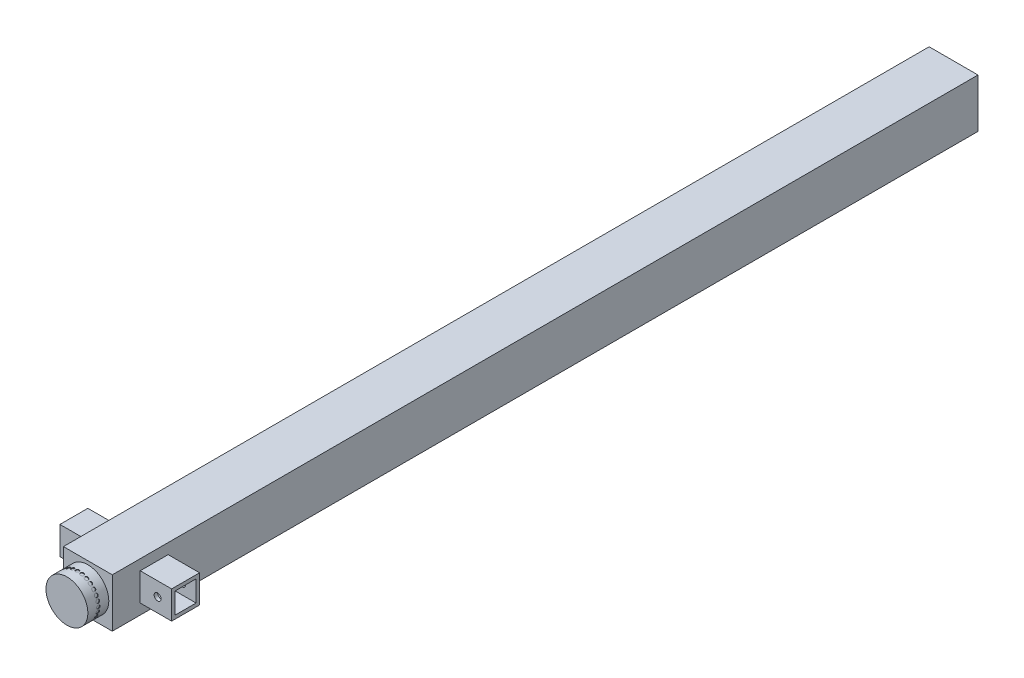
SolidWorks part; units mm, degrees
material "6061-T6 (SS)"
ref_plane "Front Plane" through (0, 0, 0) normal (0, 0, 1) x (1, 0, 0)
ref_plane "Top Plane" through (0, 0, 0) normal (0, 1, 0) x (1, 0, 0)
ref_plane "Right Plane" through (0, 0, 0) normal (1, 0, 0) x (0, 0, -1)
sketch "Sketch1" plane through (0, 0, 0) normal (0, 0, 1) x (1, 0, 0)
  line L0 (-38.1, 38.1) -> (-38.1, -38.1)
  line L1 (-44.45, 44.45) -> (44.45, 44.45)
  line L2 (-44.45, 44.45) -> (-44.45, -44.45)
  line L3 (-44.45, -44.45) -> (44.45, -44.45)
  line L4 (44.45, 44.45) -> (44.45, -44.45)
  line L5 (-44.45, 44.45) -> (44.45, -44.45) construction
  line L6 (-44.45, -44.45) -> (44.45, 44.45) construction
  line L7 (-38.1, -38.1) -> (38.1, -38.1)
  line L8 (38.1, 38.1) -> (38.1, -38.1)
  line L9 (-38.1, 38.1) -> (38.1, 38.1)
  point P0 (0, 0)
  dimension "D1" = 88.9
  dimension "D2" = 88.9
  dimension "D3" = 6.35
extrude "Boss-Extrude1" add sketch "Sketch1" against normal blind 1574.8
sketch "Sketch2" plane through (0, 44.45, 0) normal (0, 1, 0) x (1, 0, 0)
  line L0 (44.45, 1574.8) -> (44.45, 0) construction
  line L1 (-44.45, 6.35) -> (44.45, 6.35)
  line L2 (-44.45, 6.35) -> (-44.45, 0)
  line L3 (-44.45, 0) -> (44.45, 0)
  line L4 (44.45, 6.35) -> (44.45, 0)
  line L5 (-44.45, 6.35) -> (44.45, 0) construction
  line L6 (-44.45, 0) -> (44.45, 6.35) construction
  line L7 (44.45, 0) -> (-44.45, 0) construction
  line L8 (-44.45, 1574.8) -> (-44.45, 0) construction
  point P0 (0, 3.175)
  dimension "D1" = 6.35
extrude "Boss-Extrude2" add sketch "Sketch2" against normal up to surface (88.9 mm away) up to face at (0, -44.45, -787.4)
sketch "Sketch3" plane through (0, 0, 0) normal (0, 0, 1) x (1, 0, 0)
  circle A0 centre (0, 0) radius 38.1
  dimension "D1" = 76.2
extrude "Boss-Extrude3" add sketch "Sketch3" along normal blind 38.1
sketch "Sketch4" plane through (44.45, 0, 0) normal (1, 0, 0) x (0, 0, -1)
  line L0 (57.15, 19.05) -> (57.15, -19.05)
  line L1 (50.8, 25.4) -> (101.6, 25.4)
  line L2 (50.8, 25.4) -> (50.8, -25.4)
  line L3 (50.8, -25.4) -> (101.6, -25.4)
  line L4 (101.6, 25.4) -> (101.6, -25.4)
  line L5 (50.8, 25.4) -> (101.6, -25.4) construction
  line L6 (50.8, -25.4) -> (101.6, 25.4) construction
  line L7 (57.15, -19.05) -> (95.25, -19.05)
  line L8 (95.25, 19.05) -> (95.25, -19.05)
  line L9 (57.15, 19.05) -> (95.25, 19.05)
  point P0 (76.2, 0)
  point P5 (50.8, 0)
  dimension "D1" = 50.8
  dimension "D2" = 50.8
  dimension "D3" = 50.8
  dimension "D4" = 6.35
extrude "Boss-Extrude4" add sketch "Sketch4" along normal blind 57.15
sketch "Sketch5" plane through (-44.45, 0, 0) normal (-1, 0, 0) x (0, 0, 1)
  line L0 (0, 44.45) -> (0, -44.45) construction
  line L1 (-101.6, 25.4) -> (-50.8, 25.4)
  line L2 (-101.6, 25.4) -> (-101.6, -25.4)
  line L3 (-101.6, -25.4) -> (-50.8, -25.4)
  line L4 (-50.8, 25.4) -> (-50.8, -25.4)
  line L5 (-101.6, 25.4) -> (-50.8, -25.4) construction
  line L6 (-101.6, -25.4) -> (-50.8, 25.4) construction
  line L7 (-95.25, 19.05) -> (-95.25, -19.05)
  line L8 (-95.25, -19.05) -> (-57.15, -19.05)
  line L9 (-57.15, 19.05) -> (-57.15, -19.05)
  line L10 (-95.25, 19.05) -> (-57.15, 19.05)
  point P0 (-76.2, 0)
  dimension "D1" = 50.8
  dimension "D2" = 50.8
  dimension "D3" = 50.8
  dimension "D4" = 6.35
extrude "Boss-Extrude5" add sketch "Sketch5" along normal blind 57.15
sketch "Sketch7" plane through (-44.45, 0, 0) normal (-1, 0, 0) x (0, 0, 1)
  circle A0 centre (19.05, 0) radius 3.175
  dimension "D2" = 6.35
  dimension "D1" = 19.05
extrude "Cut-Extrude1" cut sketch "Sketch7" against normal blind 7.62 contours A0
pattern_curve "CrvPattern1" of "Cut-Extrude1" parameters "D1"=28, "D3"=50, "D2"=1, "D4"=50
sketch "Sketch8" plane through (0, 0, -50.8) normal (0, 0, 1) x (1, 0, 0)
  line L2 (101.6, 25.4) -> (101.6, -25.4) construction
  line L3 (-101.6, -25.4) -> (-101.6, 25.4) construction
  circle A0 centre (-76.2, 0) radius 6.35
  circle A1 centre (76.2, 0) radius 6.35
  point P4 (0, 0)
  point P6 (0, 0)
  dimension "D1" = 12.7
  dimension "D2" = 12.7
  dimension "D3" = 25.4
  dimension "D4" = 25.4
extrude "Cut-Extrude2" cut sketch "Sketch8" against normal up to surface (50.8 mm away) up to face at (-73.025, 0, -101.6)
